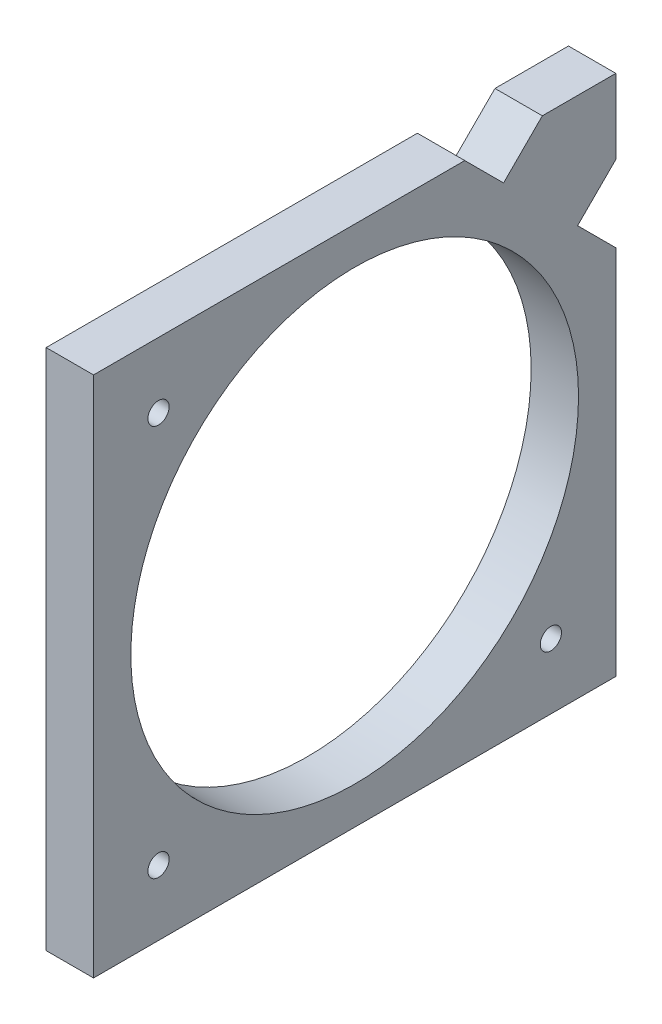
SolidWorks part; units mm, degrees
ref_plane "Front Plane" through (0, 0, 0) normal (0, 0, 1) x (1, 0, 0)
ref_plane "Top Plane" through (0, 0, 0) normal (0, 1, 0) x (1, 0, 0)
ref_plane "Right Plane" through (0, 0, 0) normal (1, 0, 0) x (0, 0, -1)
sketch "Sketch1" plane through (0, 0, 0) normal (1, 0, 0) x (0, 0, -1)
  line L0 (35, 70) -> (35, 0) construction
  line L1 (0, 0) -> (70, 0)
  line L2 (0, 0) -> (0, 70)
  line L3 (0, 70) -> (49.7566, 70)
  line L4 (70, 70) -> (70, 60.0116)
  line L5 (0, 35) -> (70, 35) construction
  line L6 (64.8725, 54.8841) -> (70, 49.7566)
  line L7 (54.9526, 64.804) -> (60.1486, 70)
  line L8 (70, 60.0116) -> (64.8725, 54.8841)
  line L10 (60.1486, 70) -> (70, 70)
  line L11 (70, 49.7566) -> (70, 0)
  line L12 (54.9526, 64.804) -> (49.7566, 70)
  circle A0 centre (35, 35) radius 30
extrude "Boss-Extrude1" add sketch "Sketch1" along normal blind 6.35
sketch "Sketch2" plane through (6.35, 0, 0) normal (1, 0, 0) x (0, 0, -1)
  line L1 (0, 35) -> (70, 35) construction
  line L3 (0, 70) -> (0, 0) construction
  line L4 (70, 0) -> (70, 49.7566) construction
  line L5 (35, 0) -> (35, 70) construction
  line L6 (0, 0) -> (70, 0) construction
  line L7 (49.7566, 70) -> (0, 70) construction
  circle A1 centre (8.7074, 61.25) radius 1.4224
  circle A2 centre (8.7074, 8.75) radius 1.4224
  circle A3 centre (61.2926, 8.75) radius 1.4224
extrude "Cut-Extrude1" cut sketch "Sketch2" against normal blind 6.35
sketch "Sketch3" plane through (6.35, 0, 0) normal (1, 0, 0) x (0, 0, -1)
  line L0 (70, 70) -> (56.2132, 56.2132)
  circle A0 centre (35, 35) radius 30 construction
